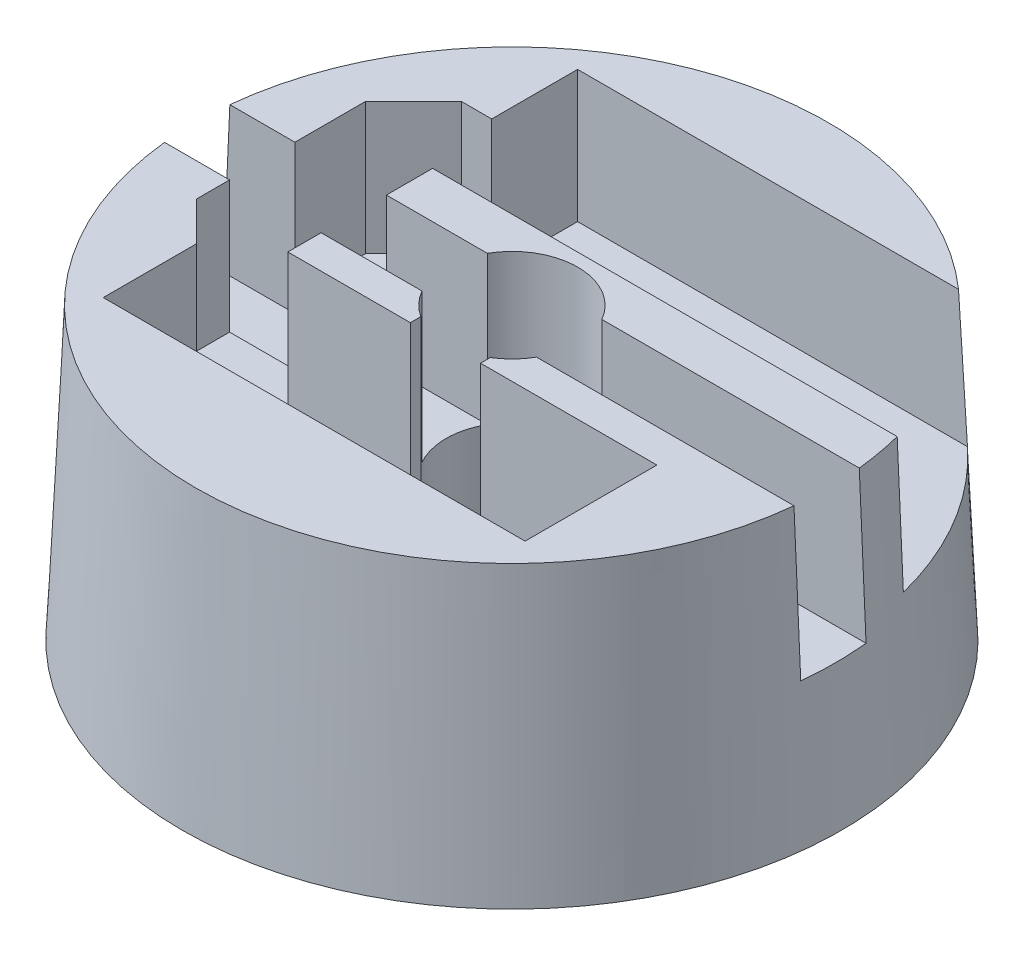
SolidWorks part; units mm, degrees
ref_plane "前视基准面" through (0, 0, 0) normal (0, 0, 1) x (1, 0, 0)
ref_plane "上视基准面" through (0, 0, 0) normal (0, 1, 0) x (1, 0, 0)
ref_plane "右视基准面" through (0, 0, 0) normal (1, 0, 0) x (0, 0, -1)
sketch "草图1" plane through (0, 0, 0) normal (0, 1, 0) x (1, 0, 0)
  circle A0 centre (0, 0) radius 12.5
  dimension "D1" = 25
ref_plane "基准面4" through (0, 11, 0) normal (0, 1, 0) x (1, 0, 0)
sketch "草图2" plane through (0, 11, 0) normal (0, 1, 0) x (1, 0, 0)
  circle A0 centre (0, 0) radius 12
  dimension "D1" = 24
loft "放样1" add profiles "草图2", "草图1"
sketch "草图4" plane through (0, 0, 0) normal (0, 1, 0) x (1, 0, 0)
  line L0 (-1.3523, -2.5) -> (-1.3523, -2.1027)
  line L1 (8, -7.5) -> (-8, -7.5)
  line L2 (8, -7.5) -> (8, -2.5)
  line L3 (8, -2.5) -> (1.3099, -2.5)
  line L4 (-8, -7.5) -> (-8, -2.5)
  line L5 (8, -7.5) -> (-8, -2.5) construction
  line L6 (8, -2.5) -> (-8, -7.5) construction
  line L7 (1.3099, -2.5) -> (1.3099, -2.1293)
  line L8 (-1.3523, -2.5) -> (-8, -2.5)
  arc A0 (1.3099, -2.1293) -> (-1.3523, -2.1027) centre (0, 0) ccw
  point P3 (0, -5)
  dimension "D1" = 5
  dimension "D2" = 16
  dimension "D3" = 5
extrude "切除-拉伸1" cut sketch "草图4" along normal through all contours A0 L0 L8 L4 L1 L2 L3 L7
sketch "草图5" plane through (0, 11, 0) normal (0, 1, 0) x (1, 0, 0)
  line L0 (6.5, 8.991) -> (15.3486, 8.991)
  line L1 (6.5, 2.991) -> (-6.5, 2.991)
  line L2 (6.5, 2.991) -> (6.5, 8.991)
  line L3 (6.5, 8.991) -> (-6.5, 8.991)
  line L4 (-6.5, 2.991) -> (-6.5, 8.991)
  line L5 (6.5, 2.991) -> (-6.5, 8.991) construction
  line L6 (6.5, 8.991) -> (-6.5, 2.991) construction
  line L7 (6.5, 2.991) -> (15.3486, 2.991)
  line L8 (15.3486, 2.991) -> (15.3486, 8.991)
  point P0 (0, 5.991)
  dimension "D1" = 13
  dimension "D2" = 6
extrude "切除-拉伸2" cut sketch "草图5" against normal blind 5
sketch "草图6" plane through (0, 0, 0) normal (1, 0, 0) x (0, 0, -1)
  line L0 (0, 17.1385) -> (0, -6.7643) construction
  line L2 (1.2383, 5.3729) -> (-1.2383, 5.3729)
  line L3 (1.2383, 5.3729) -> (1.2383, 12.2082)
  line L4 (1.2383, 12.2082) -> (-1.2383, 12.2082)
  line L5 (-1.2383, 5.3729) -> (-1.2383, 12.2082)
  line L6 (1.2383, 5.3729) -> (-1.2383, 12.2082) construction
  line L7 (1.2383, 12.2082) -> (-1.2383, 5.3729) construction
  point P3 (0, 8.7905)
extrude "切除-拉伸3" cut sketch "草图6" against normal mid plane 40
sketch "草图7" plane through (0, 11, 0) normal (0, 1, 0) x (1, 0, 0)
  line L0 (-5.9982, 2.991) -> (-5.9982, -3.9694)
  line L1 (11.6213, 2.991) -> (-6.5, 2.991) construction
  line L2 (-5.9982, -3.9694) -> (-8, -3.9694)
  line L3 (-8, -2.5) -> (-8, -7.5) construction
  line L4 (-8, -3.9694) -> (-9.4694, -2.5)
  line L5 (-9.4694, -2.5) -> (-9.4694, 3.9106)
  line L6 (-9.4694, 3.9106) -> (-7.6456, 5.7344)
  line L7 (-7.6456, 5.7344) -> (-6.5, 5.7344)
  line L8 (-6.5, 2.991) -> (-6.5, 8.991) construction
  line L9 (-6.5, 5.7344) -> (-5.9982, 2.991)
extrude "切除-拉伸4" cut sketch "草图7" against normal up to surface (5 mm away) up to face at (1.8949, 6, -6.0561)
